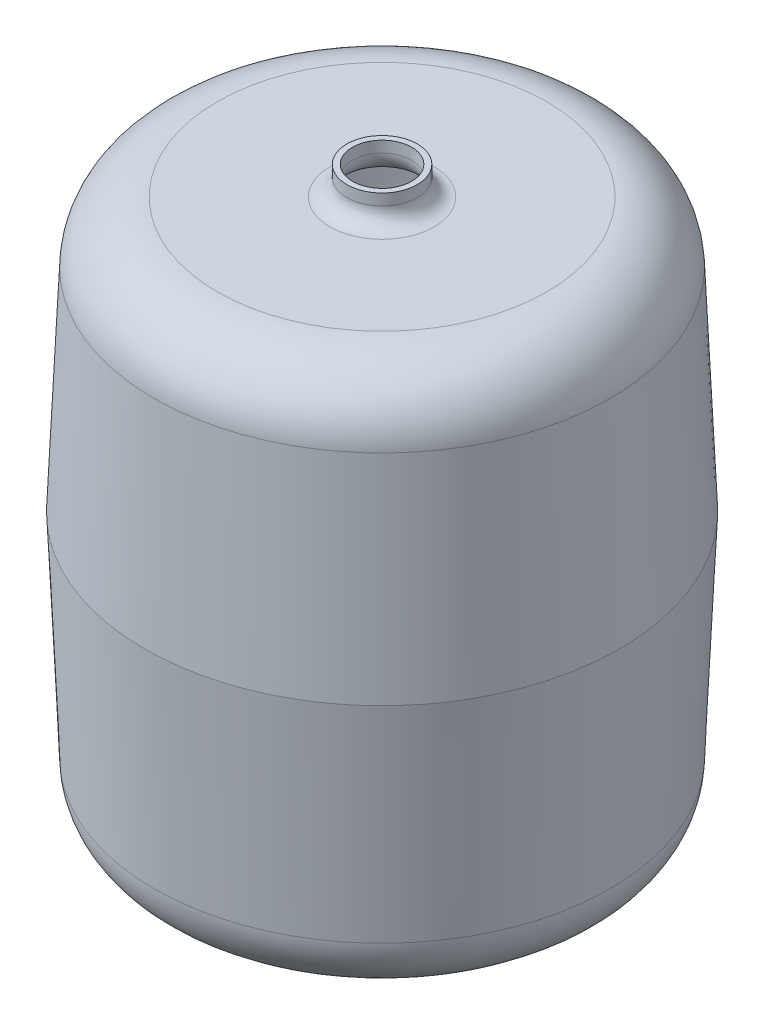
SolidWorks part; units mm, degrees
material "1060 Alloy"
ref_plane "Front Plane" through (0, 0, 0) normal (0, 0, 1) x (1, 0, 0)
ref_plane "Top Plane" through (0, 0, 0) normal (0, 1, 0) x (1, 0, 0)
ref_plane "Right Plane" through (0, 0, 0) normal (1, 0, 0) x (0, 0, -1)
sketch "Sketch1" plane through (0, 0, 0) normal (0, 0, 1) x (1, 0, 0)
  line L0 (0, 579.0191) -> (0, 0) construction
  line L1 (0, 0) -> (116.9219, 0)
  line L2 (161.879, 43.0371) -> (168.4593, 193.75)
  line L3 (168.4593, 193.75) -> (161.879, 344.4629)
  line L4 (116.9219, 387.5) -> (37, 387.5)
  line L5 (0, 407.5) -> (25, 407.5)
  line L6 (25, 407.5) -> (25, 399.5)
  line L7 (0, 403.5) -> (21, 403.5)
  line L8 (21, 403.5) -> (21, 399.5)
  line L9 (116.9219, 383.5) -> (37, 383.5)
  line L10 (164.4555, 193.75) -> (157.8828, 344.2884)
  line L11 (157.8828, 43.2116) -> (164.4555, 193.75)
  line L12 (0, 4) -> (116.9219, 4)
  line L13 (0, 407.5) -> (0, 403.5)
  line L14 (0, 4) -> (0, 0)
  arc A0 (116.9219, 0) -> (161.879, 43.0371) centre (116.9219, 45) ccw
  arc A1 (161.879, 344.4629) -> (116.9219, 387.5) centre (116.9219, 342.5) ccw
  arc A2 (25, 399.5) -> (37, 387.5) centre (37, 399.5) ccw
  arc A3 (21, 399.5) -> (37, 383.5) centre (37, 399.5) ccw
  arc A4 (157.8828, 344.2884) -> (116.9219, 383.5) centre (116.9219, 342.5) ccw
  arc A5 (116.9219, 4) -> (157.8828, 43.2116) centre (116.9219, 45) ccw
  point P7 (160, 0)
  point P13 (160, 387.5)
  point P18 (25, 387.5)
  dimension "D3" = 45
  dimension "D8" = 45
  dimension "D11" = 12
  dimension "D1" = 579.0191
  dimension "D2" = 160
  dimension "D4" = 387.5
  dimension "D5" = 92.5
  dimension "D6" = 92.5
  dimension "D7" = 193.75
  dimension "D9" = 25
  dimension "D10" = 20
  dimension "D12" = 4
revolve "Revolve1" add sketch "Sketch1" angle 360 about L0
sketch "Sketch3" plane through (0, 407.5, 0) normal (0, 1, 0) x (1, 0, 0)
  circle A0 centre (0, 0) radius 21
  dimension "D1" = 42
extrude "Cut-Extrude1" cut sketch "Sketch3" against normal blind 30
equation "\"A\"= 325mm"
equation "\"B\"= 387.50mm"
